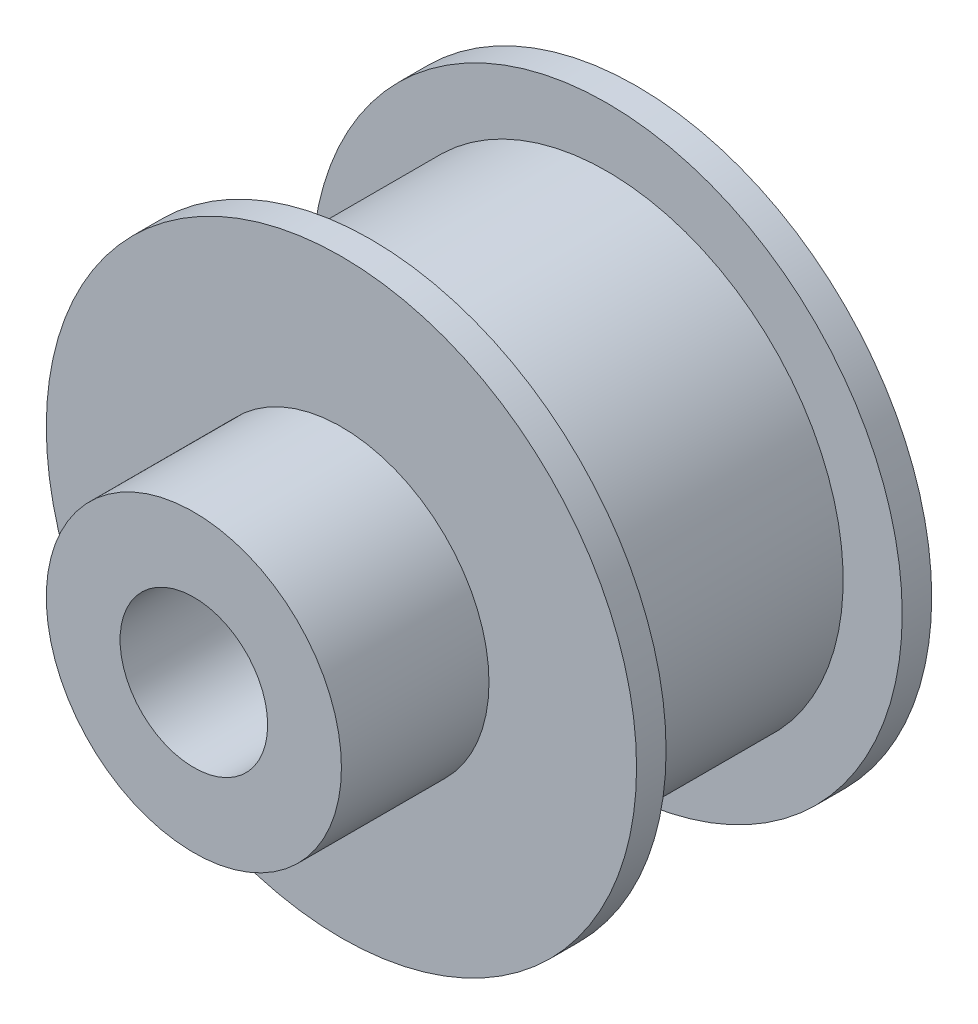
SolidWorks part; units mm, degrees
ref_plane "Plan de face" through (0, 0, 0) normal (0, 0, 1) x (1, 0, 0)
ref_plane "Plan de dessus" through (0, 0, 0) normal (0, 1, 0) x (1, 0, 0)
ref_plane "Plan de droite" through (0, 0, 0) normal (1, 0, 0) x (0, 0, -1)
sketch "Esquisse1" plane through (0, 0, 0) normal (0, 0, 1) x (1, 0, 0)
  circle A0 centre (0, 0) radius 10
  dimension "D1" = 20
extrude "Boss.-Extru.1" add sketch "Esquisse1" along normal blind 10
sketch "Esquisse2" plane through (0, 0, 10) normal (0, 0, 1) x (1, 0, 0)
  circle A0 centre (0, 0) radius 5
  dimension "D1" = 10
extrude "Boss.-Extru.2" add sketch "Esquisse2" along normal blind 5
sketch "Esquisse3" plane through (0, 0, 15) normal (0, 0, 1) x (1, 0, 0)
  circle A0 centre (0, 0) radius 2.5
  dimension "D1" = 5
extrude "Enlèv. mat.-Extru.1" cut sketch "Esquisse3" against normal through all
sketch "Esquisse4" plane through (0, 0, 0) normal (1, 0, 0) x (0, 0, -1)
  line L0 (0, 10) -> (-10, 10) construction
  line L1 (-1, 10) -> (-9, 10)
  line L2 (-1, 10) -> (-1, 8)
  line L3 (-1, 8) -> (-9, 8)
  line L4 (-9, 10) -> (-9, 8)
  line L5 (-10, 10) -> (-10, -10) construction
  line L6 (0, -10) -> (0, 10) construction
  line L7 (0, 0) -> (-3.6877, 0) construction
  dimension "D1" = 1
  dimension "D2" = 1
  dimension "D3" = 2
revolve "Enlèvement de matière-Révolution1" cut sketch "Esquisse4" angle 360 about L7
